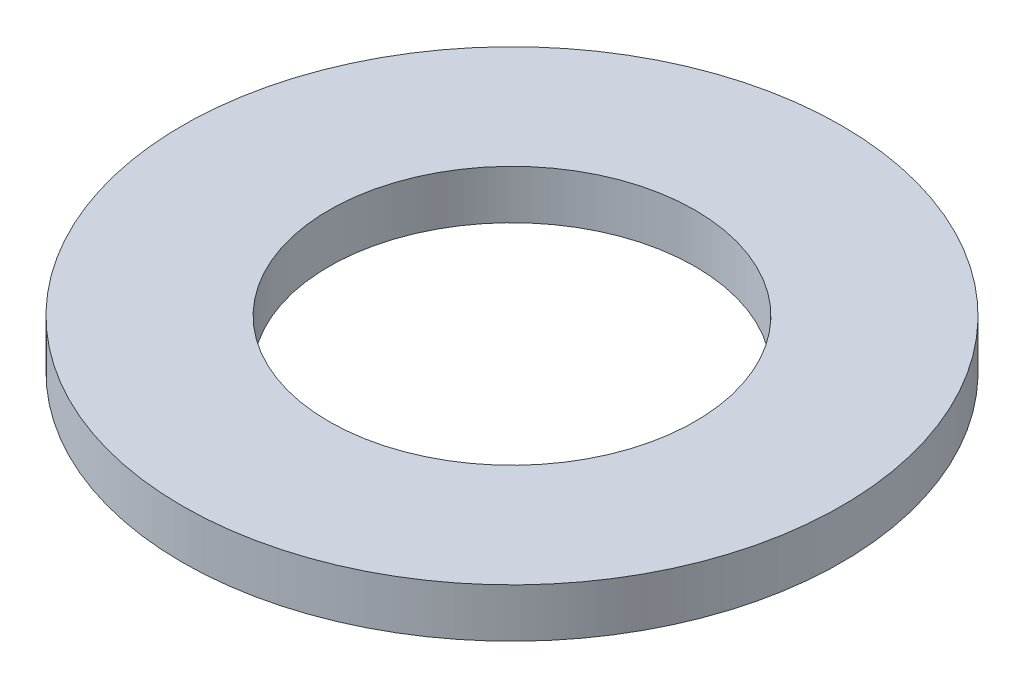
SolidWorks part; units mm, degrees
ref_plane "Plan de face" through (0, 0, 0) normal (0, 0, 1) x (1, 0, 0)
ref_plane "Plan de dessus" through (0, 0, 0) normal (0, 1, 0) x (1, 0, 0)
ref_plane "Plan de droite" through (0, 0, 0) normal (1, 0, 0) x (0, 0, -1)
sketch "Esquisse1" plane through (0, 0, 0) normal (0, 1, 0) x (1, 0, 0)
  circle A0 centre (0, 0) radius 1.35
  circle A1 centre (0, 0) radius 0.75
  dimension "D1" = 2.7
  dimension "D2" = 1.5
extrude "Extrusion1" add sketch "Esquisse1" along normal blind 0.2
